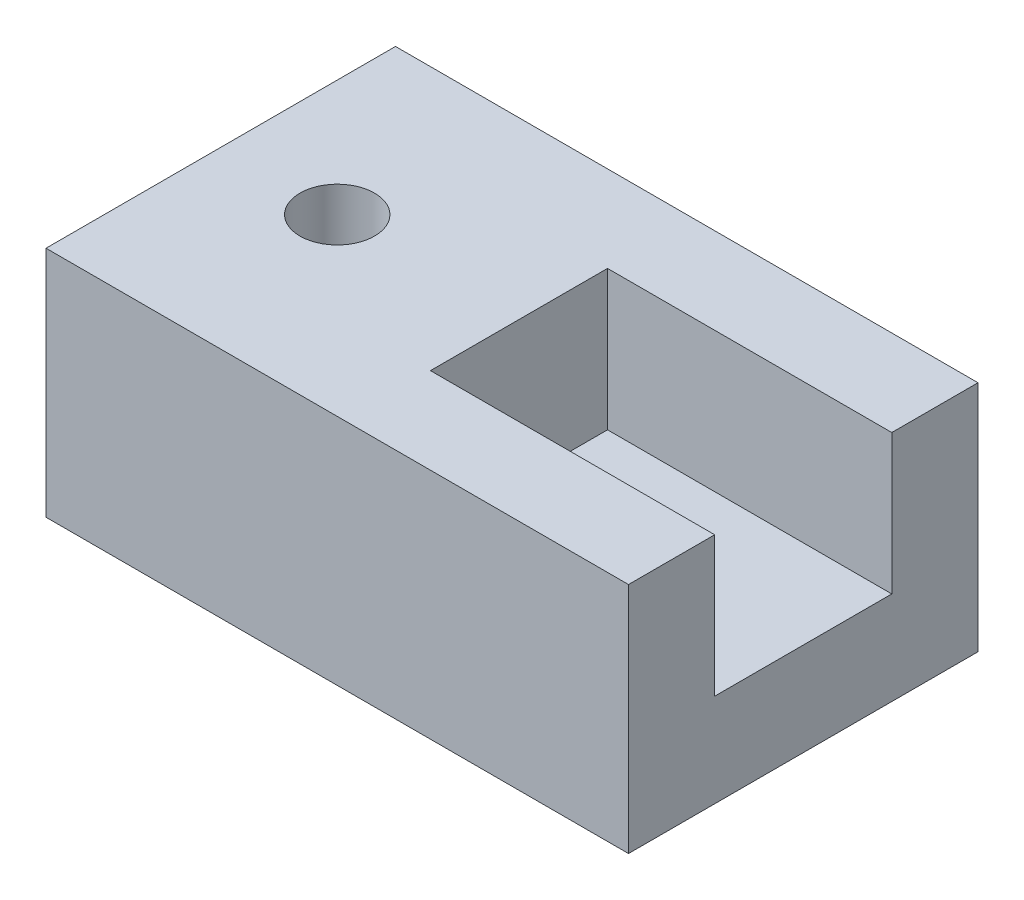
SolidWorks part; units mm, degrees
ref_plane "Спереди" through (0, 0, 0) normal (0, 0, 1) x (1, 0, 0)
ref_plane "Сверху" through (0, 0, 0) normal (0, 1, 0) x (1, 0, 0)
ref_plane "Справа" through (0, 0, 0) normal (1, 0, 0) x (0, 0, -1)
sketch "Sketch1" plane through (0, 0, 0) normal (0, 1, 0) x (1, 0, 0)
  line L1 (25, -15) -> (-25, -15)
  line L2 (25, -15) -> (25, 15)
  line L3 (25, 15) -> (-25, 15)
  line L4 (-25, -15) -> (-25, 15)
  line L5 (25, -15) -> (-25, 15) construction
  line L6 (25, 15) -> (-25, -15) construction
  point P0 (0, 0)
  dimension "D1" = 30
  dimension "D2" = 50
extrude "Boss-Extrude1" add sketch "Sketch1" along normal blind 20
sketch "Sketch3" plane through (-25, 0, 0) normal (-1, 0, 0) x (0, 0, 1)
  line L0 (-15, 14) -> (15, 14) construction
  line L1 (-15, 20) -> (-15, 0) construction
  line L2 (15, 20) -> (15, 0) construction
  line L3 (-15, 20) -> (15, 20) construction
  line L4 (7.6, 8) -> (-7.6, 8)
  line L5 (7.6, 8) -> (7.6, 20)
  line L6 (7.6, 20) -> (-7.6, 20)
  line L7 (-7.6, 8) -> (-7.6, 20)
  line L8 (7.6, 8) -> (-7.6, 20) construction
  line L9 (7.6, 20) -> (-7.6, 8) construction
  point P6 (0, 14)
  dimension "D1" = 15.2
  dimension "D2" = 12
extrude "Cut-Extrude1" cut sketch "Sketch3" against normal through all
sketch "Sketch4" plane through (0, 8, 0) normal (0, 1, 0) x (1, 0, 0)
  line L0 (25, 0) -> (-25, 0) construction
  line L1 (25, 7.6) -> (25, -7.6) construction
  line L2 (-25, 7.6) -> (-25, -7.6) construction
sketch "Sketch5" plane through (0, 8, 0) normal (0, 1, 0) x (1, 0, 0)
  line L0 (25, 7.6) -> (25, -7.6) construction
  line L1 (-25, 7.6) -> (-25, -7.6) construction
  circle A0 centre (11, 0) radius 4.2
  circle A1 centre (-15, 0) radius 3.2
  dimension "D2" = 8.4
  dimension "D3" = 6.4
  dimension "D1" = 14
  dimension "D4" = 10
extrude "Cut-Extrude2" cut sketch "Sketch5" against normal through all
sketch "Sketch6" plane through (0, 8, 0) normal (0, 1, 0) x (1, 0, 0)
  line L0 (11, -4.2) -> (11, 4.2) construction
  line L1 (0.6, 7.6) -> (-25, 7.6)
  line L2 (0.6, 7.6) -> (0.6, -7.6)
  line L3 (0.6, -7.6) -> (-25, -7.6)
  line L4 (-25, 7.6) -> (-25, -7.6)
  line L5 (0.6, 7.6) -> (-25, -7.6) construction
  line L6 (0.6, -7.6) -> (-25, 7.6) construction
  circle A0 centre (-15, 0) radius 3.2
  circle A1 centre (-15, 0) radius 3.2 construction
  circle A2 centre (11, 0) radius 4.2 construction
  point P0 (-12.2, 0)
  dimension "D1" = 10.4
extrude "Boss-Extrude2" add sketch "Sketch6" along normal up to surface (12 mm away) up to face at (0, 20, 11.3)
